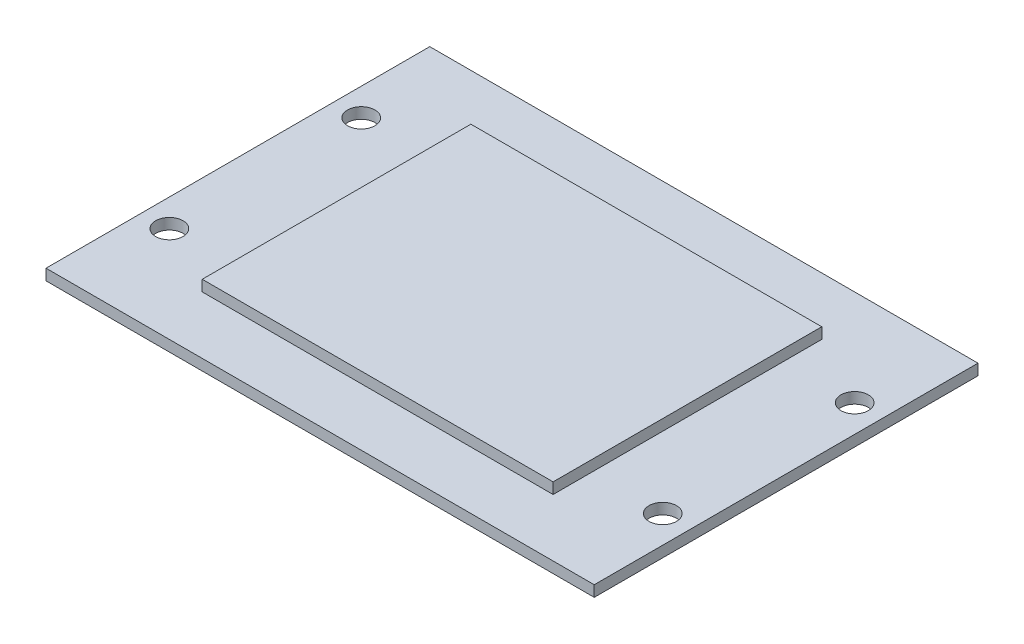
SolidWorks part; units mm, degrees
ref_plane "Front Plane" through (0, 0, 0) normal (0, 0, 1) x (1, 0, 0)
ref_plane "Top Plane" through (0, 0, 0) normal (0, 1, 0) x (1, 0, 0)
ref_plane "Right Plane" through (0, 0, 0) normal (1, 0, 0) x (0, 0, -1)
sketch "Sketch1" plane through (0, 0, 0) normal (0, 1, 0) x (1, 0, 0)
  line L1 (-47.1325, 25.0348) -> (52.8675, 25.0348)
  line L2 (-47.1325, 25.0348) -> (-47.1325, -44.9652)
  line L3 (-47.1325, -44.9652) -> (52.8675, -44.9652)
  line L4 (52.8675, 25.0348) -> (52.8675, -44.9652)
  dimension "D1" = 100
  dimension "D2" = 70
extrude "Boss-Extrude1" add sketch "Sketch1" along normal blind 2
sketch "Sketch2" plane through (0, 2, 0) normal (0, 1, 0) x (1, 0, 0)
  line L0 (52.8675, -44.9652) -> (52.8675, 25.0348) construction
  line L1 (-29.1325, -34.4652) -> (34.8675, -34.4652)
  line L2 (-29.1325, -34.4652) -> (-29.1325, 14.5348)
  line L3 (-29.1325, 14.5348) -> (34.8675, 14.5348)
  line L4 (34.8675, -34.4652) -> (34.8675, 14.5348)
  line L6 (52.8675, 25.0348) -> (-47.1325, 25.0348) construction
  point P4 (52.8675, -9.9652)
  point P5 (34.8675, -9.9652)
  point P8 (2.8675, 14.5348)
  point P9 (2.8675, 25.0348)
  dimension "D1" = 64
  dimension "D2" = 49
extrude "Boss-Extrude2" add sketch "Sketch2" along normal blind 2
sketch "Sketch3" plane through (0, 2, 0) normal (0, 1, 0) x (1, 0, 0)
  line L0 (-47.1325, -44.9652) -> (52.8675, -44.9652) construction
  line L1 (52.8675, -44.9652) -> (52.8675, 25.0348) construction
  line L2 (-47.1325, 25.0348) -> (-47.1325, -44.9652) construction
  circle A0 centre (-42.1325, 7.5348) radius 2.5
  circle A1 centre (47.8675, 7.5348) radius 2.5
  circle A2 centre (47.8675, -27.4652) radius 2.5
  circle A3 centre (-42.1325, -27.4652) radius 2.5
  point P8 (2.8675, -44.9652)
  point P11 (52.8675, -9.9652)
  point P14 (-47.1325, -9.9652)
  dimension "D4" = 5
  dimension "D1" = 90
  dimension "D2" = 35
  dimension "D3" = 35
  dimension "D5" = 90
  dimension "D6" = 45
  dimension "D7" = 17.5
  dimension "D8" = 17.5
extrude "Cut-Extrude1" cut sketch "Sketch3" against normal blind 2
